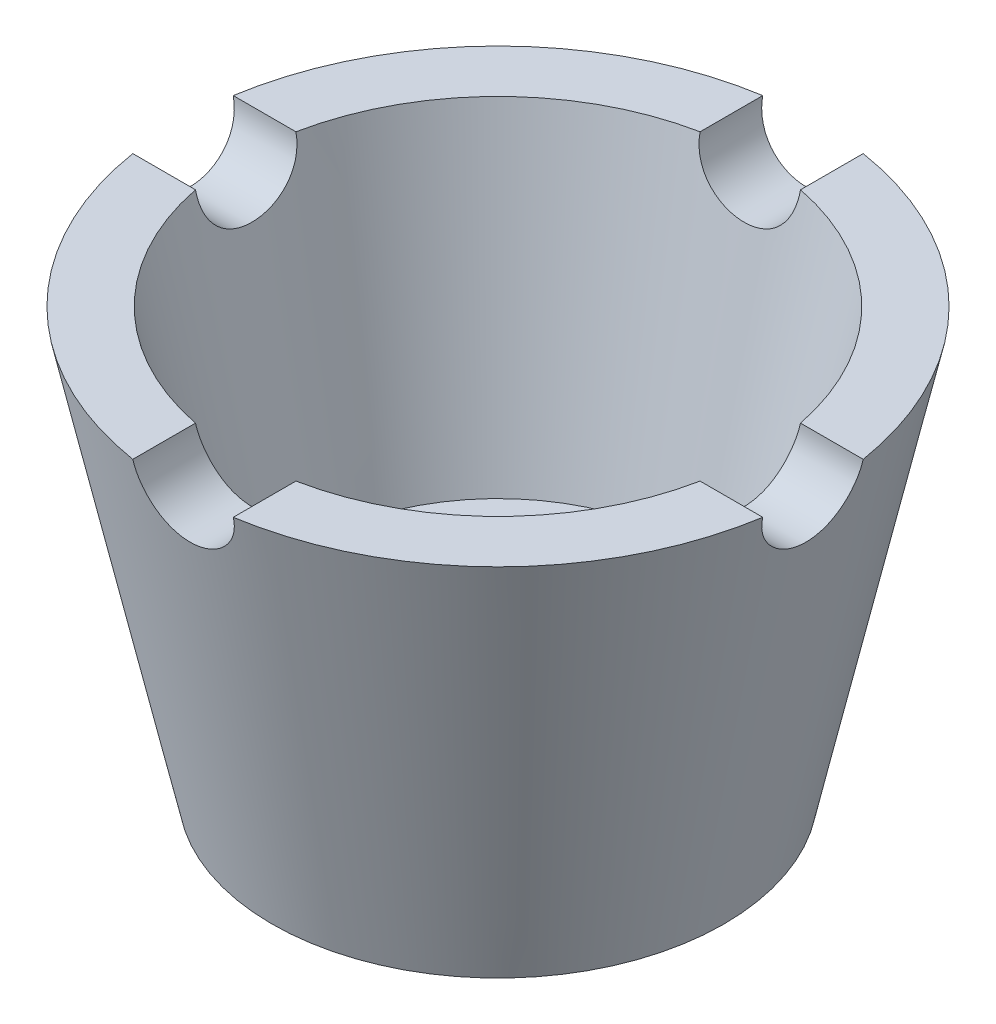
SolidWorks part; units mm, degrees
material "AISI 1020"
ref_plane "Front Plane" through (0, 0, 0) normal (0, 0, 1) x (1, 0, 0)
ref_plane "Top Plane" through (0, 0, 0) normal (0, 1, 0) x (1, 0, 0)
ref_plane "Right Plane" through (0, 0, 0) normal (1, 0, 0) x (0, 0, -1)
sketch "Sketch1" plane through (0, 0, 0) normal (0, 0, 1) x (1, 0, 0)
  line L0 (11.8808, 0) -> (22.5, 0)
  line L1 (22.5, 0) -> (31.7537, 42)
  line L2 (31.7537, 42) -> (25.6098, 42)
  line L3 (25.6098, 42) -> (19, 12)
  line L4 (19, 12) -> (11, 12)
  line L5 (11, 12) -> (11, 0)
  line L6 (11, 0) -> (11.8808, 0)
  line L7 (0, 0) -> (0, 42) construction
  point P10 (0, 0)
  dimension "D1" = 22.5
  dimension "D2" = 11
  dimension "D3" = 42
  dimension "D4" = 12
  dimension "D5" = 19
  dimension "D6" = 6
revolve "Revolve1" add sketch "Sketch1" angle 360 about L7
sketch "Sketch2" plane through (0, 0, 0) normal (0, 0, 1) x (1, 0, 0)
  line L0 (31.7537, 42) -> (-31.7537, 42) construction
  circle A0 centre (0, 42) radius 5
extrude "Cut-Extrude1" cut sketch "Sketch2" against normal mid plane 71
pattern_circular "CirPattern1" count 4 over 360 about axis through (0, 0, 0) along (0, 1, 0) of "Cut-Extrude1"
